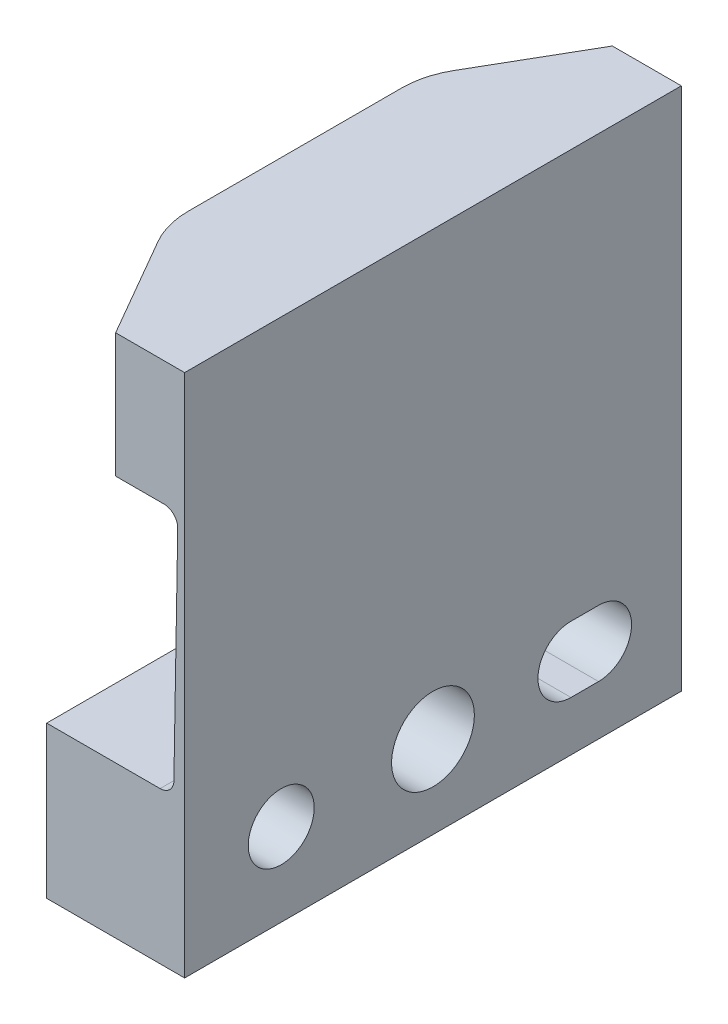
SolidWorks part; units mm, degrees
material "Ti-6Al-4VSolution treated and aged (SS)"
ref_plane "Front Plane" through (0, 0, 0) normal (0, 0, 1) x (1, 0, 0)
ref_plane "Top Plane" through (0, 0, 0) normal (0, 1, 0) x (1, 0, 0)
ref_plane "Right Plane" through (0, 0, 0) normal (1, 0, 0) x (0, 0, -1)
sketch "Sketch4" plane through (0, 0, 0) normal (0, 0, 1) x (1, 0, 0)
  line L0 (0, 19.5) -> (0, 14.5)
  line L1 (0, 14.5) -> (4.2501, 14.5)
  line L2 (4.75, 13.9913) -> (4.6104, 5.9913)
  line L3 (4.1104, 5.5) -> (0, 5.5)
  line L4 (0, 5.5) -> (0, 0)
  line L5 (0, 0) -> (5, 0)
  line L6 (5, 0) -> (5, 19.5)
  line L7 (5, 19.5) -> (0, 19.5)
  arc A0 (4.6104, 5.9913) -> (4.1104, 5.5) centre (4.1104, 6) cw
  arc A1 (4.2501, 14.5) -> (4.75, 13.9913) centre (4.2501, 14) cw
  dimension "D7" = 1
  dimension "D6" = 0.5
  dimension "D4" = 0.5
  dimension "D1" = 5.5
  dimension "D2" = 19.5
  dimension "D3" = 5
  dimension "D5" = 5
  dimension "D8" = 0.25
extrude "Boss-Extrude1" add sketch "Sketch4" along normal blind 9
chamfer "Chamfer1" distance 2.5 angle 60 1 edges at (0, 17, 9)
fillet "Fillet1" radius 3 1 edges at (0, 17, 4.6699)
mirror "Mirror1" about plane through (4.2501, 14, 0) normal (0, 0, -1) of bodies 103 104
sketch "Sketch11" plane through (5, 0, 0) normal (1, 0, 0) x (0, 0, -1)
  line L0 (0, 0) -> (0, 3) construction
  line L1 (-9, 0) -> (9, 0) construction
  line L2 (-5.5, 3) -> (5.5, 3) construction
  line L3 (5, 3) -> (6, 3) construction
  line L4 (5, 4.1956) -> (6, 4.1956)
  line L5 (5, 1.8044) -> (6, 1.8044)
  circle A0 centre (-5.5, 3) radius 1.1956
  circle A2 centre (0, 3) radius 1.5
  circle A3 centre (0, 3) radius 3 construction
  arc A4 (5, 4.1956) -> (5, 1.8044) centre (5, 3) ccw
  arc A5 (6, 1.8044) -> (6, 4.1956) centre (6, 3) ccw
  point P12 (5.5, 3)
  dimension "D3" = 3
  dimension "D4" = 2.3913
  dimension "D5" = 6
  dimension "D6" = 1
  dimension "D1" = 11
  dimension "D2" = 3
extrude "Cut-Extrude1" cut sketch "Sketch11" against normal through all
sketch "Sketch12" plane through (0, 19.5, 0) normal (0, 1, 0) x (1, 0, 0)
  line L6 (0, 3.866) -> (0, -3.866)
  line L7 (0.4019, -5.366) -> (2.5, -9)
  line L8 (2.5, -9) -> (5, -9)
  line L9 (5, -9) -> (5, 9)
  line L10 (5, 9) -> (2.5, 9)
  line L11 (2.5, 9) -> (0.4019, 5.366)
  line L12 (0, 3.866) -> (0, -3.866)
  line L13 (0.4019, -5.366) -> (2.5, -9)
  line L14 (2.5, -9) -> (5, -9)
  line L15 (5, -9) -> (5, 9)
  line L16 (5, 9) -> (2.5, 9)
  line L17 (2.5, 9) -> (0.4019, 5.366)
  arc A2 (0, -3.866) -> (0.4019, -5.366) centre (3, -3.866) ccw
  arc A3 (0.4019, 5.366) -> (0, 3.866) centre (3, 3.866) ccw
  arc A4 (0, -3.866) -> (0.4019, -5.366) centre (3, -3.866) ccw
  arc A5 (0.4019, 5.366) -> (0, 3.866) centre (3, 3.866) ccw
  dimension "D1" = 0
extrude "Cut-Extrude2" cut sketch "Sketch12" against normal blind 0.5
